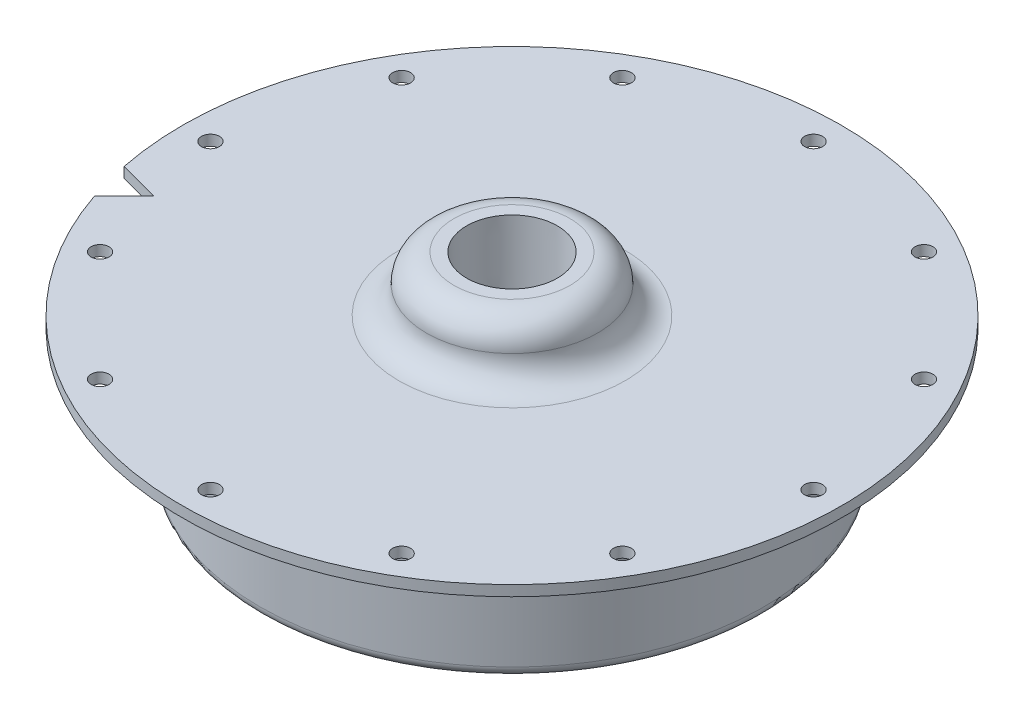
SolidWorks part; units mm, degrees
material "6063-T6"
ref_plane "Front Plane" through (0, 0, 0) normal (0, 0, 1) x (1, 0, 0)
ref_plane "Top Plane" through (0, 0, 0) normal (0, 1, 0) x (1, 0, 0)
ref_plane "Right Plane" through (0, 0, 0) normal (1, 0, 0) x (0, 0, -1)
ref_axis "Axis1" through (0, 55, 0) along (0, -1, 0)
sketch "Sketch1" plane through (0, 0, 0) normal (0, 0, 1) x (1, 0, 0)
  line L0 (-49.784, 0) -> (-39.6875, 0)
  line L1 (0, 55) -> (0, -55) construction
  line L2 (-49.784, 0) -> (-49.784, 1.5875)
  line L3 (-5.588, 9.906) -> (-8.763, 9.906)
  line L5 (-5.588, 9.906) -> (-5.588, 0)
  line L6 (-5.588, 0) -> (0, 0) construction
  line L7 (-49.784, 0) -> (-49.784, 1.5875) construction
  line L8 (-5.588, 1.5875) -> (-5.588, 0) construction
  line L9 (-38.1, -1.5875) -> (-38.1, -17.4625)
  line L11 (-34.925, -17.4625) -> (-34.925, -3.175)
  line L12 (-31.75, 0) -> (-5.588, 0)
  line L13 (0, -201000) -> (0, 249000) construction
  line L14 (-49.784, 1.5875) -> (-17.0815, 1.5875)
  arc A0 (-34.925, -3.175) -> (-31.75, 0) centre (-31.75, -3.175) cw
  arc A1 (-38.1, -1.5875) -> (-39.6875, 0) centre (-39.6875, -1.5875) ccw
  arc A2 (-17.0815, 1.5875) -> (-12.9223, 5.7467) centre (-17.0815, 5.7467) ccw
  arc A3 (-8.763, 9.906) -> (-12.9223, 5.7467) centre (-8.763, 5.7467) ccw
  arc A4 (-38.1, -17.4625) -> (-34.925, -17.4625) centre (-36.5125, -17.4625) ccw
  point P18 (-34.925, 0)
  dimension "D4" = 3.175
  dimension "D5" = 1.5875
  dimension "D1" = 3.175
  dimension "D2" = 38.1
  dimension "D3" = 17.4625
  dimension "D6" = 1.5875
  dimension "D7" = 3.175
  dimension "D8" = 9.906
revolve "Revolve1" add sketch "Sketch1" angle 360 about axis through (0, 55, 0) along (0, -1, 0)
ref_plane "Hole Location Plane" through (0, 3.175, 0) normal (0, 1, 0) x (1, 0, 0)
sketch "Hole Location" plane through (0, 3.175, 0) normal (0, 1, 0) x (1, 0, 0)
  line L0 (0, 0) -> (-45.5549, 0) construction
  circle A0 centre (0, 0) radius 45.5549 construction
  dimension "D1" = 91.1098
hole_wizard "#36 (0.1065) Diameter Hole1" positions "Sketch2" profile "Sketch3" hole size "#36" standard "ANSI Inch" end condition through all
sketch "Sketch2" plane through (0, 1.5875, 0) normal (0, 1, 0) x (1, 0, 0)
  point P0 (-45.5549, 0)
sketch "Sketch3" plane through (-45.5549, 1.5875, 0) normal (1, 0, 0) x (0, 0, 1)
  line L0 (0, 0) -> (0, 20.6375)
  line L1 (0, 20.6375) -> (1.3525, 20.6375)
  line L2 (1.3525, 20.6375) -> (1.3525, 0)
  line L5 (1.3525, 0) -> (0, 0)
  line L11 (0, -6.35) -> (0, 107.95) construction
  dimension "Thru Hole Dia." = 2.7051
  dimension "Thru Hole Depth" = 20.6375
pattern_circular "CirPattern1" count 12 over 360 about axis through (0, 0, 0) along (0, 1, 0) of "#36 (0.1065) Diameter Hole1"
hole_wizard "1/4 NPT Tapped Hole1" positions "Sketch4" profile "Sketch5" size "1/4" standard "ANSI Inch" end condition through all
sketch "Sketch4" plane through (0, 9.906, 0) normal (0, 1, 0) x (1, 0, 0)
  point P0 (0, 0)
sketch "Sketch5" plane through (0, 9.906, 0) normal (1, 0, 0) x (0, 0, 1)
  line L0 (0, 0) -> (0, 28.956)
  line L1 (0, 28.956) -> (5.5626, 28.956)
  line L2 (-6.558, 9.906) -> (-6.8546, 0) construction
  line L3 (5.5626, 28.956) -> (5.5626, 9.906)
  line L4 (5.5626, 9.906) -> (6.558, 9.906)
  line L5 (6.558, 9.906) -> (6.8546, 0)
  line L7 (6.8546, 0) -> (0, 0)
  line L8 (0, -6.35) -> (0, 107.95) construction
  line L11 (-5.5626, 9.906) -> (-6.558, 9.906) construction
  dimension "Thru Tap Drill Dia." = 11.1252
  dimension "Thru Tap Drill Depth" = 28.956
  dimension "Thread Dia." = 13.7092
  dimension "Thread Angle" = 3.43
  dimension "Thread Depth" = 9.906
sketch "Sketch6" plane through (0, 1.5875, 0) normal (0, 1, 0) x (1, 0, 0)
  line L0 (0, 0) -> (-48.0877, -12.885) construction
  line L1 (0, 0) -> (-45.5549, 0) construction
  line L2 (-47.168, -15.9256) -> (-42.6779, -11.4355)
  line L3 (-42.6779, -11.4355) -> (-48.8115, -9.792)
  circle A0 centre (0, 0) radius 49.784 construction
  arc A1 (-47.168, -15.9256) -> (-48.8115, -9.792) centre (0, 0) cw
  circle M16 centre (0, 0) radius 49.784
  dimension "D1" = 15
  dimension "D2" = 60
  dimension "D3" = 6.35
extrude "Cut-Extrude1" cut sketch "Sketch6" against normal up to surface (1.5875 mm away) contours L2 L0 A1 | L0 L3 M16 up to face at (-39.4517, 0, -24.13)
equation "\"D1@Hole Location\"=\"TANK DIAMETER@Cryo Tank.Assembly\"+\"GASKET SEAT THICKNESS@Cryo Tank.Assembly\"+\"LINER THICKNESS@Cryo Tank.Assembly\"+\"SHRINK FIT DELTA@Cryo Tank.Assembly\""
equation "\"D2@Sketch1\"=\"TANK DIAMETER@Cryo Tank.Assembly\"/2"
equation "\"D3@Sketch1\"=0.5+0.125+0.0625"
